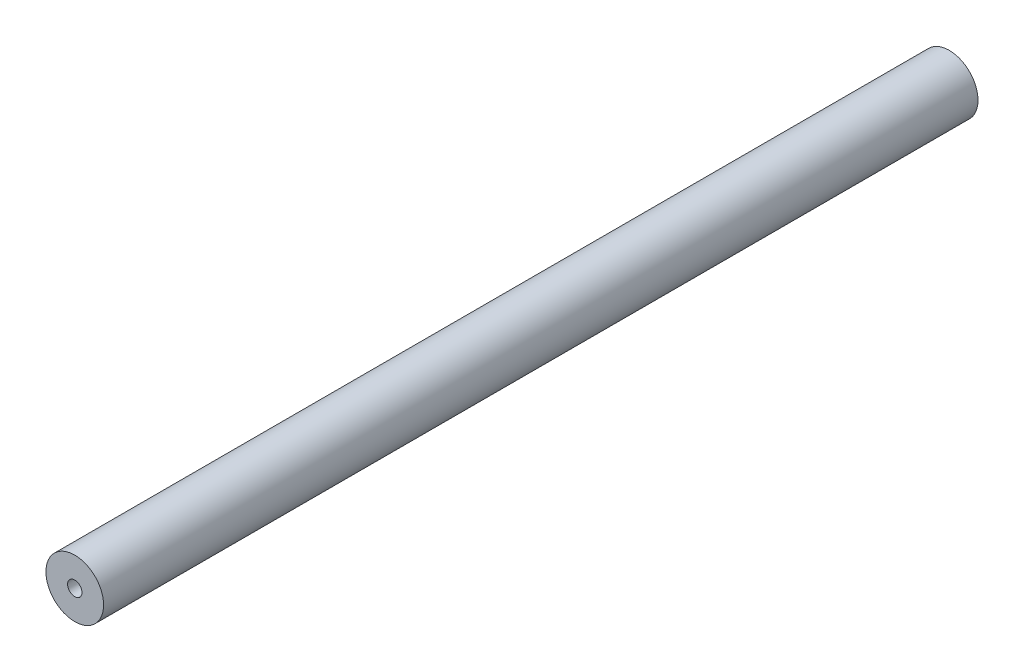
SolidWorks part; units mm, degrees
material "1060 合金"
ref_plane "正面" through (0, 0, 0) normal (0, 0, 1) x (1, 0, 0)
ref_plane "平面" through (0, 0, 0) normal (0, 1, 0) x (1, 0, 0)
ref_plane "右側面" through (0, 0, 0) normal (1, 0, 0) x (0, 0, -1)
sketch "ｽｹｯﾁ1" plane through (0, 0, 0) normal (0, 0, 1) x (1, 0, 0)
  circle A0 centre (0, 0) radius 6
extrude "ﾎﾞｽ - 押し出し1" add sketch "ｽｹｯﾁ1" along normal blind 182
sketch "ｽｹｯﾁ2" plane through (0, 0, 182) normal (0, 0, 1) x (1, 0, 0)
  circle A0 centre (0, 0) radius 1.5
extrude "ｶｯﾄ - 押し出し1" cut sketch "ｽｹｯﾁ2" against normal blind 8.8
sketch "ｽｹｯﾁ7" plane through (0, 0, 0) normal (0, 0, -1) x (-1, 0, 0)
  circle A0 centre (0, 0) radius 1.5
extrude "ｶｯﾄ - 押し出し2" cut sketch "ｽｹｯﾁ7" against normal blind 8.8
